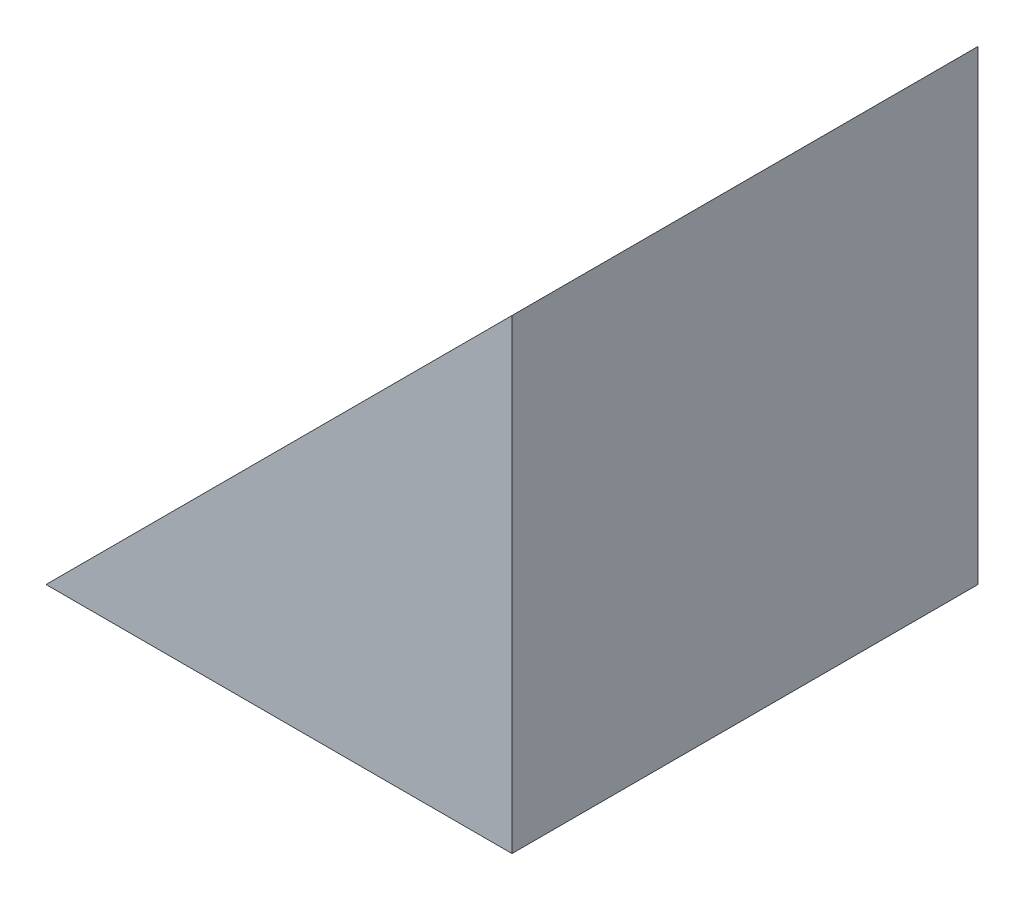
SolidWorks part; units mm, degrees
ref_plane "前视基准面" through (0, 0, 0) normal (0, 0, 1) x (1, 0, 0)
ref_plane "上视基准面" through (0, 0, 0) normal (0, 1, 0) x (1, 0, 0)
ref_plane "右视基准面" through (0, 0, 0) normal (1, 0, 0) x (0, 0, -1)
sketch "草图1" plane through (0, 0, 0) normal (0, 0, 1) x (1, 0, 0)
  line L0 (104.8284, 79.6674) -> (104.8284, 109.6674)
  line L1 (104.8284, 79.6674) -> (74.8284, 79.6674)
  line L2 (74.8284, 79.6674) -> (104.8284, 109.6674)
  dimension "D1" = 30
  dimension "D2" = 30
extrude "凸台-拉伸1" add sketch "草图1" along normal blind 30
